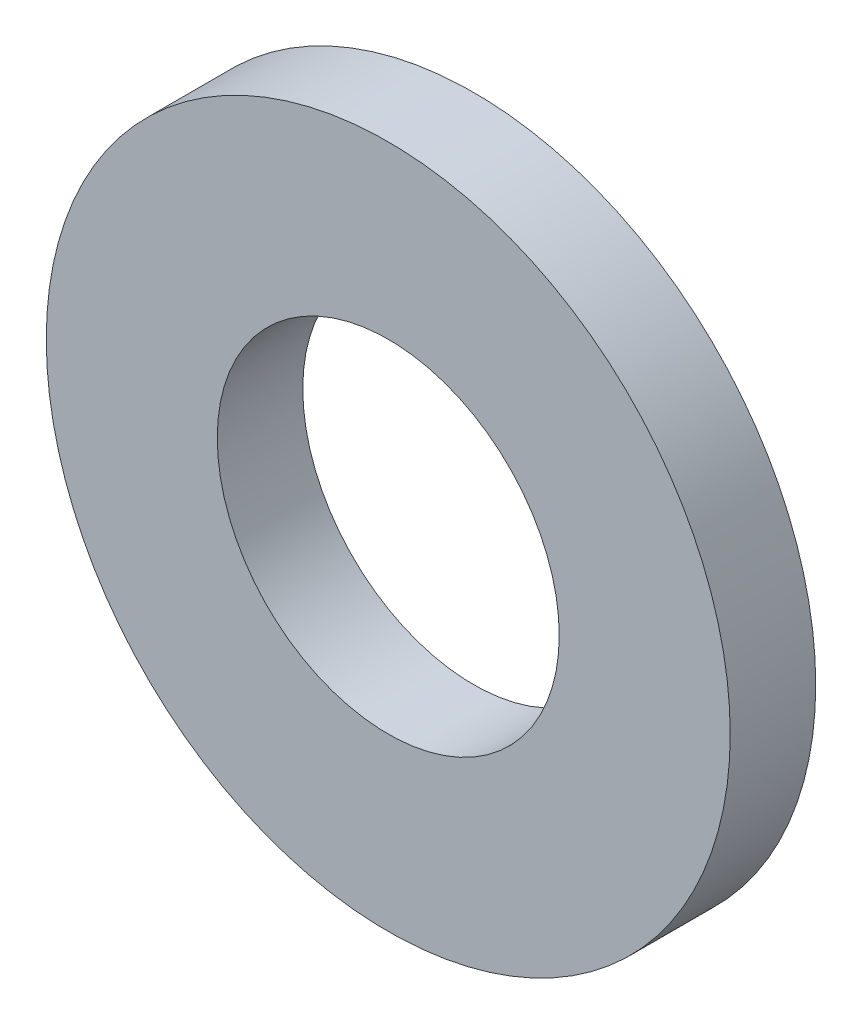
SolidWorks part; units mm, degrees
ref_plane "Front Plane" through (0, 0, 0) normal (0, 0, 1) x (1, 0, 0)
ref_plane "Top Plane" through (0, 0, 0) normal (0, 1, 0) x (1, 0, 0)
ref_plane "Right Plane" through (0, 0, 0) normal (1, 0, 0) x (0, 0, -1)
sketch "Sketch1" plane through (0, 0, 0) normal (0, 0, 1) x (1, 0, 0)
  circle A0 centre (0, 0) radius 3.175
  circle A1 centre (0, 0) radius 6.35
  dimension "D1" = 6.35
  dimension "D2" = 12.7
extrude "Boss-Extrude1" add sketch "Sketch1" along normal blind 1.5875
